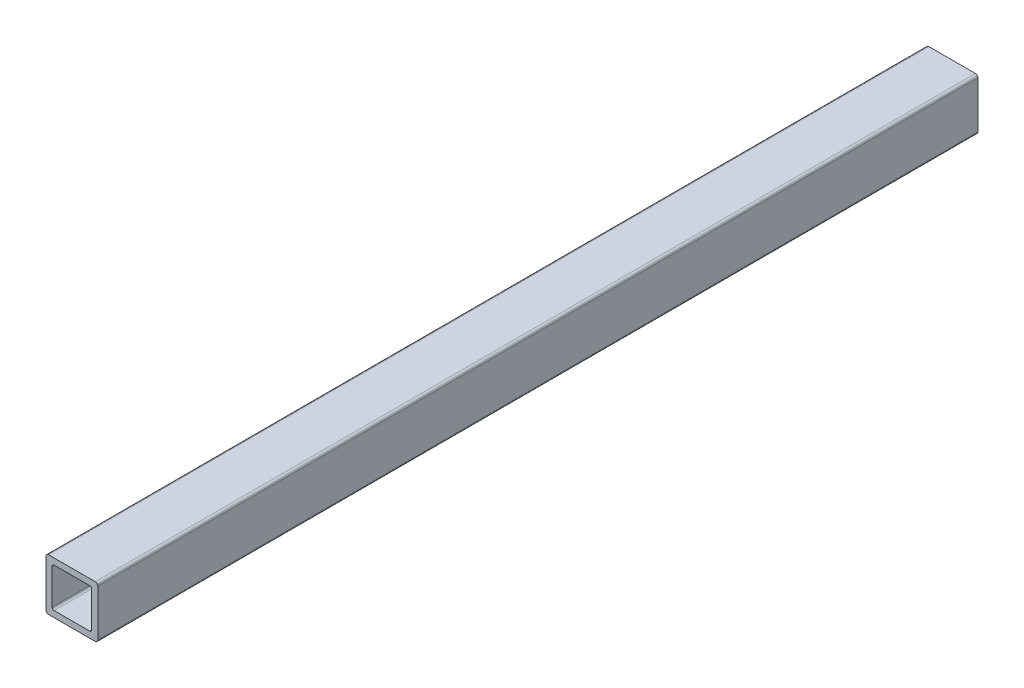
SolidWorks part; units mm, degrees
ref_plane "Front" through (0, 0, 0) normal (0, 0, 1) x (1, 0, 0)
ref_plane "Top" through (0, 0, 0) normal (0, 1, 0) x (1, 0, 0)
ref_plane "Right" through (0, 0, 0) normal (1, 0, 0) x (0, 0, -1)
sketch "Sketch1" plane through (0, 0, 0) normal (0, 0, 1) x (1, 0, 0)
  line L0 (-9.652, 0) -> (-12.7, 0) construction
  line L1 (11.43, -12.7) -> (-11.43, -12.7)
  line L2 (12.7, -11.43) -> (12.7, 11.43)
  line L3 (11.43, 12.7) -> (-11.43, 12.7)
  line L4 (-12.7, -11.43) -> (-12.7, 11.43)
  line L5 (12.7, -12.7) -> (-12.7, 12.7) construction
  line L6 (12.7, 12.7) -> (-12.7, -12.7) construction
  line L7 (8.6868, 9.652) -> (-8.6868, 9.652)
  line L8 (9.652, 8.6868) -> (9.652, -8.6868)
  line L9 (8.6868, -9.652) -> (-8.6868, -9.652)
  line L10 (-9.652, 8.6868) -> (-9.652, -8.6868)
  line L11 (9.652, 9.652) -> (-9.652, -9.652) construction
  line L12 (9.652, -9.652) -> (-9.652, 9.652) construction
  line L13 (0, -9.652) -> (0, -12.7) construction
  line L14 (9.652, -8.6868) -> (9.652, -12.7) construction
  line L16 (9.652, -12.7) -> (12.7, -12.7) construction
  arc A0 (-8.6868, -9.652) -> (-9.652, -8.6868) centre (-8.6868, -8.6868) cw
  arc A1 (9.652, -8.6868) -> (8.6868, -9.652) centre (8.6868, -8.6868) cw
  arc A2 (8.6868, 9.652) -> (9.652, 8.6868) centre (8.6868, 8.6868) cw
  arc A3 (-8.6868, 9.652) -> (-9.652, 8.6868) centre (-8.6868, 8.6868) ccw
  arc A4 (11.43, -12.7) -> (12.7, -11.43) centre (11.43, -11.43) ccw
  arc A5 (12.7, 11.43) -> (11.43, 12.7) centre (11.43, 11.43) ccw
  arc A6 (-11.43, 12.7) -> (-12.7, 11.43) centre (-11.43, 11.43) ccw
  arc A7 (-11.43, -12.7) -> (-12.7, -11.43) centre (-11.43, -11.43) cw
  point P0 (0, 0)
  point P6 (0, 0)
  dimension "D2" = 0.9652
  dimension "D3" = 1.27
sketch "Sketch2" plane through (0, 0, 0) normal (1, 0, 0) x (0, 0, -1)
  line L0 (-914.4, 0) -> (914.4, 0) construction
  dimension "Length" = 1828.8
ref_plane "Plane1" through (12.7, 0, 0) normal (1, 0, 0) x (0, 0, -1)
sketch "Sketch5" plane through (12.7, 0, 0) normal (1, 0, 0) x (0, 0, -1)
  line L0 (-914.4, 12.7) -> (-914.4, -12.7) construction
  line L1 (914.4, 12.7) -> (914.4, -12.7) construction
sketch "Sketch4" plane through (0, 0, 0) normal (0, 0, 1) x (1, 0, 0)
  line L0 (12.7, -11.43) -> (12.7, 11.43) construction
  line L1 (11.43, 12.7) -> (-11.43, 12.7) construction
  line L2 (-12.7, -11.43) -> (-12.7, 11.43) construction
  line L3 (11.43, -12.7) -> (-11.43, -12.7) construction
  line L4 (9.652, 8.6868) -> (9.652, -8.6868) construction
  line L5 (8.6868, -9.652) -> (-8.6868, -9.652) construction
  line L6 (-9.652, 8.6868) -> (-9.652, -8.6868) construction
  line L7 (8.6868, 9.652) -> (-8.6868, 9.652) construction
  line L8 (12.7, -11.43) -> (12.7, 11.43)
  line L9 (11.43, 12.7) -> (-11.43, 12.7)
  line L10 (-12.7, -11.43) -> (-12.7, 11.43)
  line L11 (11.43, -12.7) -> (-11.43, -12.7)
  line L12 (9.652, 8.6868) -> (9.652, -8.6868)
  line L13 (8.6868, -9.652) -> (-8.6868, -9.652)
  line L14 (-9.652, 8.6868) -> (-9.652, -8.6868)
  line L15 (8.6868, 9.652) -> (-8.6868, 9.652)
  arc A0 (12.7, 11.43) -> (11.43, 12.7) centre (11.43, 11.43) ccw construction
  arc A1 (-11.43, 12.7) -> (-12.7, 11.43) centre (-11.43, 11.43) ccw construction
  arc A2 (-12.7, -11.43) -> (-11.43, -12.7) centre (-11.43, -11.43) ccw construction
  arc A3 (11.43, -12.7) -> (12.7, -11.43) centre (11.43, -11.43) ccw construction
  arc A4 (8.6868, -9.652) -> (9.652, -8.6868) centre (8.6868, -8.6868) ccw construction
  arc A5 (-9.652, -8.6868) -> (-8.6868, -9.652) centre (-8.6868, -8.6868) ccw construction
  arc A6 (-8.6868, 9.652) -> (-9.652, 8.6868) centre (-8.6868, 8.6868) ccw construction
  arc A7 (9.652, 8.6868) -> (8.6868, 9.652) centre (8.6868, 8.6868) ccw construction
  arc A8 (12.7, 11.43) -> (11.43, 12.7) centre (11.43, 11.43) ccw
  arc A9 (-11.43, 12.7) -> (-12.7, 11.43) centre (-11.43, 11.43) ccw
  arc A10 (-12.7, -11.43) -> (-11.43, -12.7) centre (-11.43, -11.43) ccw
  arc A11 (11.43, -12.7) -> (12.7, -11.43) centre (11.43, -11.43) ccw
  arc A12 (8.6868, -9.652) -> (9.652, -8.6868) centre (8.6868, -8.6868) ccw
  arc A13 (-9.652, -8.6868) -> (-8.6868, -9.652) centre (-8.6868, -8.6868) ccw
  arc A14 (-8.6868, 9.652) -> (-9.652, 8.6868) centre (-8.6868, 8.6868) ccw
  arc A15 (9.652, 8.6868) -> (8.6868, 9.652) centre (8.6868, 8.6868) ccw
extrude "Boss-Extrude1" add sketch "Sketch4" along normal blind 431.8
equation "\"D3@Sketch1\"=\"Outside Width@Sketch1\"*.05"
equation "\"D2@Sketch1\"=\"D1@Sketch1\"*.05"
